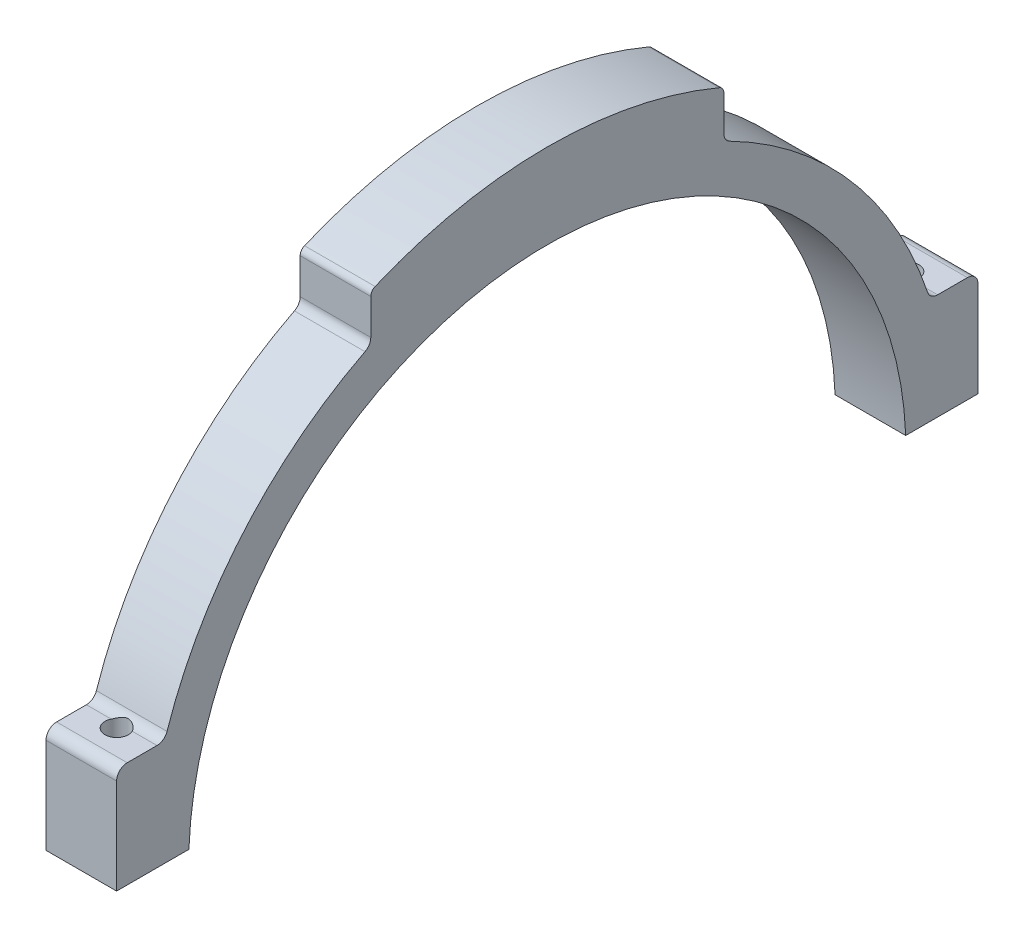
SolidWorks part; units mm, degrees
material "Plain Carbon Steel"
ref_plane "Front Plane" through (0, 0, 0) normal (0, 0, 1) x (1, 0, 0)
ref_plane "Top Plane" through (0, 0, 0) normal (0, 1, 0) x (1, 0, 0)
ref_plane "Right Plane" through (0, 0, 0) normal (1, 0, 0) x (0, 0, -1)
sketch "Sketch1" plane through (0, 0, 0) normal (1, 0, 0) x (0, 0, -1)
  line L0 (0, 56.8) -> (0, 64.8)
  line L2 (-61, 2.0155) -> (-50.76, 2.0155)
  line L3 (50.76, 2.0155) -> (61, 2.0155)
  line L4 (-61, 2.0155) -> (-61, 15.5155)
  line L5 (-59.5, 17.0155) -> (-55.2817, 17.0155)
  line L6 (61, 2.0155) -> (61, 15.5155)
  line L7 (59.5, 17.0155) -> (55.2817, 17.0155)
  line L8 (25, 58.7762) -> (25, 51.9292)
  line L9 (-25, 58.7762) -> (-25, 51.9292)
  arc A0 (50.76, 2.0155) -> (-50.76, 2.0155) centre (0, 0) ccw
  arc A1 (53.8593, 18.0392) -> (25.8182, 50.5931) centre (0, 0) ccw
  circle A2 centre (0, 0) radius 56.8 construction
  circle A3 centre (0, 0) radius 50.8 construction
  arc A4 (-61, 15.5155) -> (-59.5, 17.0155) centre (-59.5, 15.5155) cw
  arc A5 (-55.2817, 17.0155) -> (-53.8593, 18.0392) centre (-55.2817, 18.5155) ccw
  arc A6 (55.2817, 17.0155) -> (53.8593, 18.0392) centre (55.2817, 18.5155) cw
  arc A7 (61, 15.5155) -> (59.5, 17.0155) centre (59.5, 15.5155) ccw
  arc A8 (24.0569, 60.169) -> (-24.0569, 60.169) centre (0, 0) ccw
  arc A9 (61.4452, 20.5799) -> (-61.4452, 20.5799) centre (0, 0) ccw construction
  arc A10 (-25.8182, 50.5931) -> (-53.8593, 18.0392) centre (0, 0) ccw
  arc A11 (53.8593, 18.0392) -> (-53.8593, 18.0392) centre (0, 0) ccw construction
  arc A12 (-25, 51.9292) -> (-25.8182, 50.5931) centre (-26.5, 51.9292) cw
  arc A13 (-24.0569, 60.169) -> (-25, 58.7762) centre (-23.5, 58.7762) ccw
  arc A14 (24.0569, 60.169) -> (25, 58.7762) centre (23.5, 58.7762) cw
  arc A15 (25, 51.9292) -> (25.8182, 50.5931) centre (26.5, 51.9292) ccw
  arc A16 (25, 57.6094) -> (-25, 57.6094) centre (0, 0) ccw
  arc A17 (23.3144, 58.3119) -> (-23.3144, 58.3119) centre (0, 0) ccw construction
  point P32 (-25, 51.0024)
  point P39 (25, 51.0024)
  dimension "D1" = 101.6
  dimension "D2" = 1.5
  dimension "D7" = 1.5
  dimension "D3" = 8
  dimension "D6" = 25
  dimension "D9" = 122
  dimension "D10" = 10.24
  dimension "D11" = 10.24
  dimension "D12" = 15
  dimension "D13" = 15
  dimension "D4" = 8
  dimension "D5" = 6
  dimension "D8" = 2
extrude "Boss-Extrude1" add sketch "Sketch1" along normal blind 10
hole_wizard "M4 Tapped Hole1" positions "Sketch5" profile "Sketch4" tap size "M4" standard "ISO" end condition through all
sketch "Sketch5" plane through (0, 2.0155, 0) normal (0, 1, 0) x (1, 0, 0)
  line L3 (10, -61) -> (0, -61) construction
  line L4 (0, -61) -> (0, -50.76) construction
  line L5 (10, 50.76) -> (10, 61) construction
  line L6 (10, 61) -> (0, 61) construction
  point P0 (5, 56)
  point P11 (5, -56)
  dimension "D1" = 5
  dimension "D2" = 5
  dimension "D3" = 5
  dimension "D4" = 5
cosmetic thread "Hole Thread3" parameters "D2"=4
cosmetic thread "Hole Thread4" parameters "D2"=4
sketch "Sketch4" plane through (5, 2.0155, -56) normal (1, 0, 0) x (0, 0, -1)
  line L0 (0, 0) -> (0, 60.7845)
  line L1 (0, 60.7845) -> (1.65, 60.7845)
  line L2 (1.65, 60.7845) -> (1.65, 0)
  line L5 (1.65, 0) -> (0, 0)
  line L11 (0, -6.35) -> (0, 107.95) construction
  dimension "Thru Tap Drill Dia." = 3.3
  dimension "Thru Tap Drill Depth" = 60.7845
fillet "Fillet1" radius 1 2 edges at (5, 57.6094, -25) (5, 57.6094, 25)
